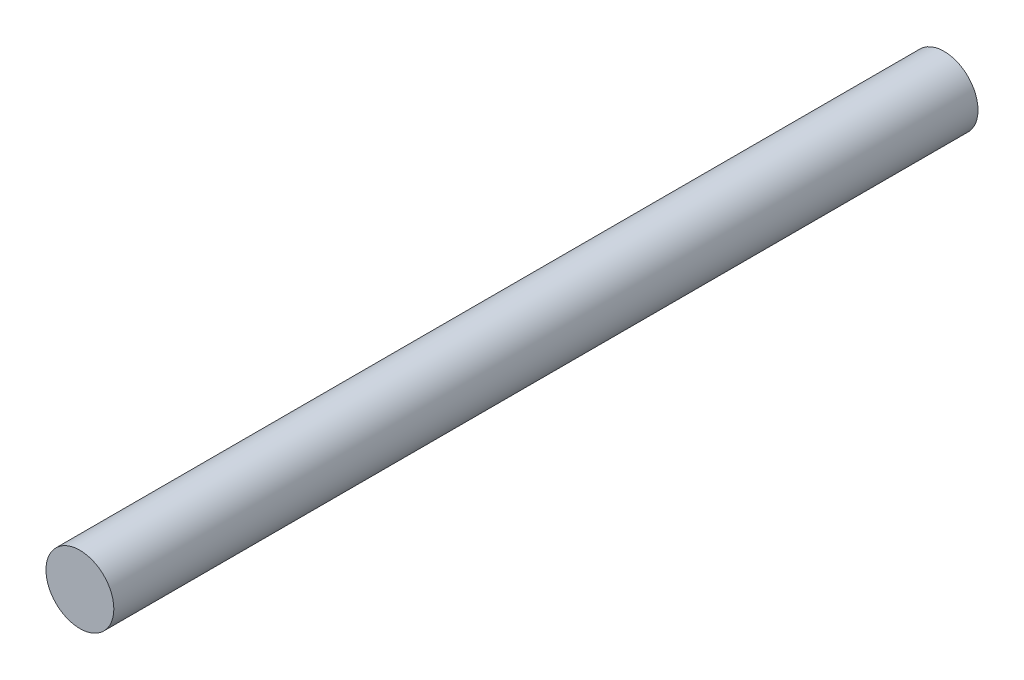
SolidWorks part; units mm, degrees
ref_plane "Plan de face" through (0, 0, 0) normal (0, 0, 1) x (1, 0, 0)
ref_plane "Plan de dessus" through (0, 0, 0) normal (0, 1, 0) x (1, 0, 0)
ref_plane "Plan de droite" through (0, 0, 0) normal (1, 0, 0) x (0, 0, -1)
sketch "Esquisse1" plane through (0, 0, 0) normal (0, 0, 1) x (1, 0, 0)
  circle A0 centre (-5.3157, -0.6241) radius 2.75
  dimension "D1" = 5.5
extrude "Boss.-Extru.1" add sketch "Esquisse1" along normal blind 70
